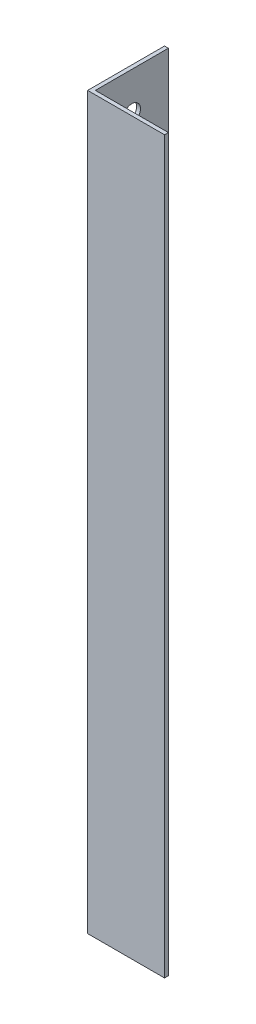
SolidWorks part; units mm, degrees
material "1060 Сплав"
ref_plane "Спереди" through (0, 0, 0) normal (0, 0, 1) x (1, 0, 0)
ref_plane "Сверху" through (0, 0, 0) normal (0, 1, 0) x (1, 0, 0)
ref_plane "Справа" through (0, 0, 0) normal (1, 0, 0) x (0, 0, -1)
sketch "Эскиз1" plane through (0, 0, 0) normal (0, 1, 0) x (1, 0, 0)
  line L0 (0, 0) -> (0, 20)
  line L1 (0, 20) -> (1, 20)
  line L2 (1, 20) -> (1, 1)
  line L3 (1, 1) -> (20, 1)
  line L4 (20, 1) -> (20, 0)
  line L5 (20, 0) -> (0, 0)
  dimension "D1" = 1
  dimension "D2" = 20
extrude "Бобышка-Вытянуть1" add sketch "Эскиз1" along normal blind 190
sketch "Эскиз2" plane through (1, 0, 0) normal (1, 0, 0) x (0, 0, -1)
  line L0 (10.5, 190) -> (10.5, 0) construction
  line L1 (1, 190) -> (20, 190) construction
  line L2 (1, 0) -> (20, 0) construction
  circle A0 centre (10.5, 10) radius 2.25
  circle A1 centre (10.5, 180) radius 2.25
  dimension "D1" = 4.5
  dimension "D2" = 10
  dimension "D3" = 4.5
  dimension "D4" = 10
extrude "Вырез-Вытянуть1" cut sketch "Эскиз2" against normal through all
sketch "Эскиз3" plane through (0, 0, 0) normal (-1, 0, 0) x (0, 0, 1)
  circle A0 centre (-10.5, 159.5) radius 2.25 construction
  circle A1 centre (-10.5, 159.5) radius 2.25
extrude "Вырез-Вытянуть2" cut sketch "Эскиз3" against normal through all
